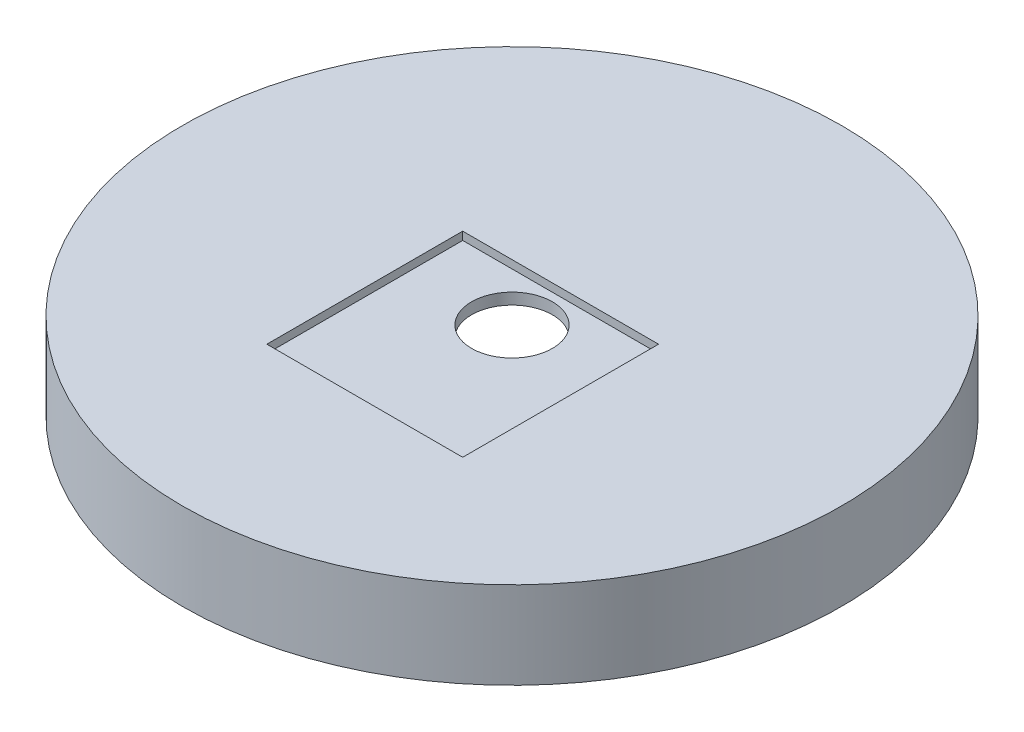
SolidWorks part; units mm, degrees
ref_plane "Front Plane" through (0, 0, 0) normal (0, 0, 1) x (1, 0, 0)
ref_plane "Top Plane" through (0, 0, 0) normal (0, 1, 0) x (1, 0, 0)
ref_plane "Right Plane" through (0, 0, 0) normal (1, 0, 0) x (0, 0, -1)
sketch "Sketch3" plane through (0, 0, 0) normal (0, 0, 1) x (1, 0, 0)
  line L0 (0, 0) -> (22, 0) construction
  line L1 (0, 6.35) -> (22, 6.35) construction
  line L2 (22, 0) -> (3.25, 5.4429)
  line L3 (3.25, -13.9932) -> (3.25, 1.2597) construction
  line L4 (0, 0) -> (0, -13.9932) construction
  line L5 (22, 0) -> (26.5, 0)
  line L6 (3.25, 7) -> (3.25, 5.4429)
  line L9 (26.5, 7) -> (26.5, 0)
  line L11 (26.5, 7) -> (3.25, 7)
  line L12 (3.25, 5.4429) -> (3.25, 7) construction
  dimension "D1" = 22
  dimension "D2" = 7
  dimension "D3" = 3.25
  dimension "D4" = 4.5
  dimension "D5" = 5.4429
revolve "Revolve1" add sketch "Sketch3" angle 360 about L4
sketch "Sketch for side slot DNU" plane through (0, 0, 0) normal (0, 0, 1) x (1, 0, 0)
  line L0 (0, 0) -> (0, 18.8028) construction
  line L1 (0, 0) -> (-24.5114, 0) construction
  line L2 (-7.874, 8.382) -> (7.874, 8.382)
  line L3 (-7.874, 8.382) -> (-7.874, 9.398)
  line L4 (-7.874, 9.398) -> (7.874, 9.398)
  line L5 (7.874, 8.382) -> (7.874, 9.398)
  line L6 (-7.874, 8.382) -> (7.874, 9.398) construction
  line L7 (-7.874, 9.398) -> (7.874, 8.382) construction
  point P3 (0, 8.89)
  dimension "D1" = 15.748
  dimension "D2" = 1.016
  dimension "D3" = 8.89
ref_plane "Plane4" through (0, 12.7, 0) normal (0, 1, 0) x (1, 0, 0)
sketch "Sketch5" plane through (0, 12.7, 0) normal (0, 1, 0) x (1, 0, 0)
  line L0 (0, 0) -> (35.335, 0) construction
  line L1 (0, 0) -> (0, 26.2568) construction
  line L2 (7.874, 3.91) -> (-7.874, 3.91)
  line L3 (-7.874, 3.91) -> (-7.874, -11.838)
  line L4 (-7.874, -11.838) -> (7.874, -11.838)
  line L5 (7.874, -11.838) -> (7.874, 3.91)
  point P7 (0, 3.91)
  dimension "D1" = 15.748
  dimension "D2" = 15.748
  dimension "D3" = 3.91
extrude "Cut-Extrude1" cut sketch "Sketch5" against normal blind 6.35
